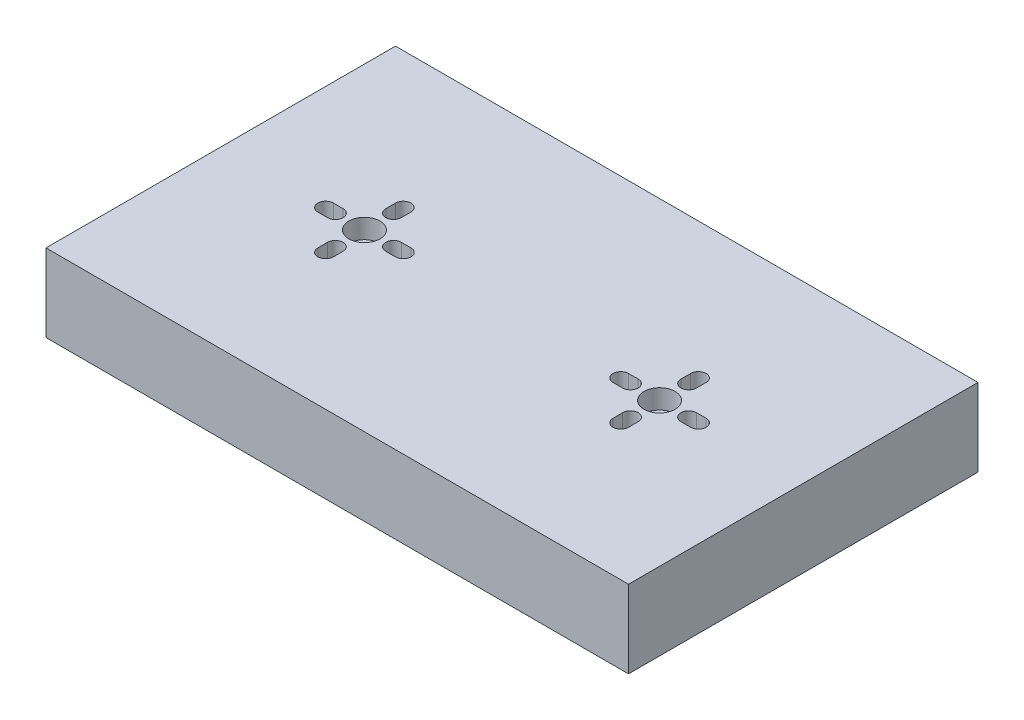
SolidWorks part; units mm, degrees
ref_plane "Front Plane" through (0, 0, 0) normal (0, 0, 1) x (1, 0, 0)
ref_plane "Top Plane" through (0, 0, 0) normal (0, 1, 0) x (1, 0, 0)
ref_plane "Right Plane" through (0, 0, 0) normal (1, 0, 0) x (0, 0, -1)
sketch "Sketch2" plane through (0, 0, 0) normal (0, 1, 0) x (1, 0, 0)
  line L1 (-75, 45) -> (75, 45)
  line L2 (-75, 45) -> (-75, -45)
  line L3 (-75, -45) -> (75, -45)
  line L4 (75, 45) -> (75, -45)
  point P4 (0, 0)
  point P5 (0, 0)
  point P8 (0, 0)
  point P10 (0, 0)
  dimension "D1" = 90
  dimension "D2" = 150
  dimension "D3" = 45
  dimension "D4" = 75
extrude "Boss-Extrude1" add sketch "Sketch2" along normal blind 20 contours L2 L1 L4 L3
sketch "Sketch3" plane through (0, 20, 0) normal (0, 1, 0) x (1, 0, 0)
  line L0 (-75, 45) -> (75, 45) construction
  line L1 (0, 0) -> (0, -22.7043) construction
  circle A0 centre (-38, 0) radius 4
  circle A1 centre (38, 0) radius 4
  dimension "D1" = 8
  dimension "D2" = 38
  dimension "D3" = 45
extrude "Cut-Extrude1" cut sketch "Sketch3" against normal blind 5
sketch "Sketch4" plane through (0, 20, 0) normal (0, 1, 0) x (1, 0, 0)
  line L0 (-45.5, 0) -> (-30.5, 0) construction
  line L1 (-38, 7.5) -> (-38, -7.5) construction
  line L2 (-48, 0) -> (-28, 0) construction
  line L3 (-38, -10) -> (-38, 10) construction
  line L4 (-48, 2) -> (-45.5, 2)
  line L5 (-48, -2) -> (-45.5, -2)
  line L6 (-48, 0) -> (-45.5, 0) construction
  line L7 (-48, 2.0064) -> (-45.5, 2.0064)
  line L8 (-48, -2.0064) -> (-45.5, -2.0064)
  line L9 (-38, 10) -> (-38, 7.5) construction
  line L10 (-36, 10) -> (-36, 7.5)
  line L11 (-40, 10) -> (-40, 7.5)
  line L12 (-30.5, 0) -> (-28, 0) construction
  line L13 (-30.5, 2) -> (-28, 2)
  line L14 (-30.5, -2) -> (-28, -2)
  line L15 (-38, -10) -> (-38, -7.5) construction
  line L16 (-40, -10) -> (-40, -7.5)
  line L17 (-36, -10) -> (-36, -7.5)
  line L18 (0, 0) -> (0, -7.5) construction
  line L19 (48, 0) -> (45.5, 0) construction
  line L20 (48, 2.0064) -> (45.5, 2.0064)
  line L21 (48, -2.0064) -> (45.5, -2.0064)
  line L22 (38, 10) -> (38, 7.5) construction
  line L23 (36, 10) -> (36, 7.5)
  line L24 (40, 10) -> (40, 7.5)
  line L25 (30.5, 0) -> (28, 0) construction
  line L26 (30.5, 2) -> (28, 2)
  line L27 (30.5, -2) -> (28, -2)
  line L28 (38, -10) -> (38, -7.5) construction
  line L29 (40, -10) -> (40, -7.5)
  line L30 (36, -10) -> (36, -7.5)
  circle A0 centre (-45.5, 0) radius 2 construction
  circle A1 centre (-30.5, 0) radius 2 construction
  circle A2 centre (-38, 7.5) radius 2 construction
  circle A3 centre (-38, -7.5) radius 2 construction
  circle A4 centre (-38, -7.5) radius 2 construction
  circle A5 centre (-30.5, 0) radius 2 construction
  circle A6 centre (-45.5, 0) radius 2 construction
  circle A7 centre (-38, 7.5) radius 2 construction
  circle A8 centre (-38, 10) radius 2 construction
  circle A9 centre (-38, -10) radius 2 construction
  circle A10 centre (-48, 0) radius 2 construction
  circle A11 centre (-28, 0) radius 2 construction
  arc A12 (-48, 2.0064) -> (-48, -2.0064) centre (-48, 0) ccw
  arc A13 (-45.5, -2.0064) -> (-45.5, 2.0064) centre (-45.5, 0) ccw
  arc A14 (-36, 10) -> (-40, 10) centre (-38, 10) ccw
  arc A15 (-40, 7.5) -> (-36, 7.5) centre (-38, 7.5) ccw
  arc A16 (-30.5, 2) -> (-30.5, -2) centre (-30.5, 0) ccw
  arc A17 (-28, -2) -> (-28, 2) centre (-28, 0) ccw
  arc A18 (-40, -10) -> (-36, -10) centre (-38, -10) ccw
  arc A19 (-36, -7.5) -> (-40, -7.5) centre (-38, -7.5) ccw
  arc A20 (48, 2.0064) -> (48, -2.0064) centre (48, 0) cw
  arc A21 (45.5, -2.0064) -> (45.5, 2.0064) centre (45.5, 0) cw
  arc A22 (36, 10) -> (40, 10) centre (38, 10) cw
  arc A23 (40, 7.5) -> (36, 7.5) centre (38, 7.5) cw
  arc A24 (30.5, 2) -> (30.5, -2) centre (30.5, 0) cw
  arc A25 (28, -2) -> (28, 2) centre (28, 0) cw
  arc A26 (40, -10) -> (36, -10) centre (38, -10) cw
  arc A27 (36, -7.5) -> (40, -7.5) centre (38, -7.5) cw
  point P8 (-38, 0)
  point P20 (-38, 0)
  point P23 (-38, 0)
  point P32 (-46.75, 0)
  point P37 (-38, 8.75)
  point P42 (-29.25, 0)
  point P47 (-38, -8.75)
  point P57 (46.75, 0)
  point P64 (38, 8.75)
  point P71 (29.25, 0)
  point P78 (38, -8.75)
  point P83 (0, 0)
  dimension "D1" = 4
  dimension "D2" = 4
  dimension "D3" = 4
  dimension "D4" = 4
  dimension "D5" = 15
  dimension "D6" = 15
  dimension "D8" = 20
  dimension "D9" = 20
  dimension "D10" = 4
  dimension "D11" = 4
  dimension "D12" = 4
  dimension "D7" = 0
extrude "Cut-Extrude2" cut sketch "Sketch4" against normal through all
equation "\"D2@Sketch3\"=32+6"
